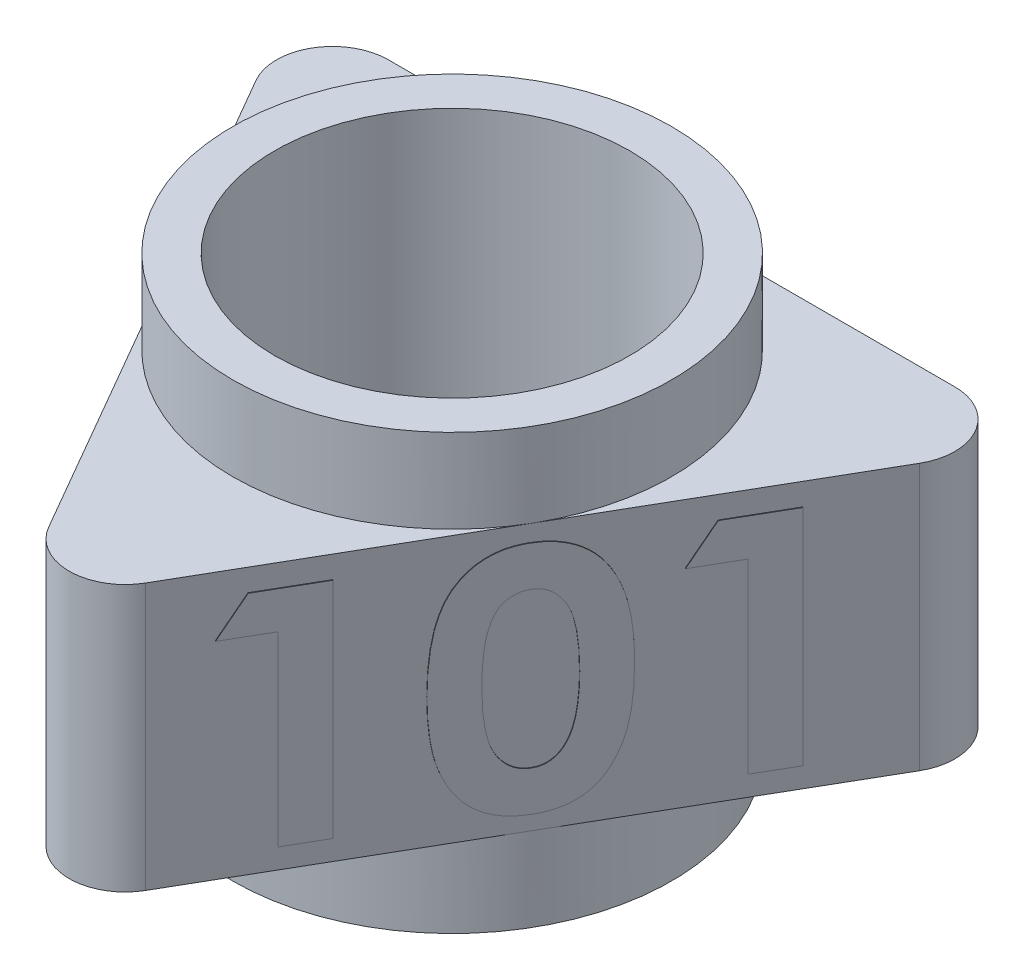
SolidWorks part; units mm, degrees
ref_plane "Front Plane" through (0, 0, 0) normal (0, 0, 1) x (1, 0, 0)
ref_plane "Top Plane" through (0, 0, 0) normal (0, 1, 0) x (1, 0, 0)
ref_plane "Right Plane" through (0, 0, 0) normal (1, 0, 0) x (0, 0, -1)
sketch "Sketch1" plane through (0, 0, 0) normal (0, 1, 0) x (1, 0, 0)
  line L1 (0, -15.7) -> (13.5966, 7.85)
  line L2 (13.5966, 7.85) -> (-13.5966, 7.85)
  line L3 (-13.5966, 7.85) -> (0, -15.7)
  circle A0 centre (0, 0) radius 6.35
  circle A1 centre (0, 0) radius 7.85 construction
  dimension "D1" = 1.5
  dimension "D2" = 12.7
extrude "Boss-Extrude1" add sketch "Sketch1" along normal mid plane 9.525
fillet "Fillet1" radius 2 3 edges at (13.5966, 0, -7.85) (-13.5966, 0, -7.85) (0, 0, 15.7)
sketch "Sketch2" plane through (6.7983, 0, 3.925) normal (0.866, 0, 0.5) x (0.5, 0, -0.866)
  line L0 (-10.1325, -4.0305) -> (10.1325, -4.0305) construction
  line L1 (-10.1325, 4.7625) -> (-10.1325, -4.7625) construction
  line L2 (10.1325, -4.7625) -> (10.1325, 4.7625) construction
  text T0 "101" font "Century Gothic" height 8
extrude "Boss-Extrude2" add sketch "Sketch2" along normal blind 0.0254
ref_axis "Axis1" through (0, 5.2388, 0) along (0, -1, 0)
pattern_circular "CirPattern1" count 3 over 360 about axis through (0, 5.2388, 0) along (0, -1, 0) of "Boss-Extrude2"
sketch "Sketch3" plane through (0, 4.7625, 0) normal (0, 1, 0) x (1, 0, 0)
  line L0 (-11.8645, 4.85) -> (-1.7321, -12.7) construction
  circle A0 centre (0, 0) radius 6.35 construction
  circle A1 centre (0, 0) radius 6.35
  circle A2 centre (0, 0) radius 7.85
extrude "Boss-Extrude3" add sketch "Sketch3" along normal blind 3 and the other way offset from surface (12.525 mm away) 3 other way up to face at (0, -4.7625, 0)
